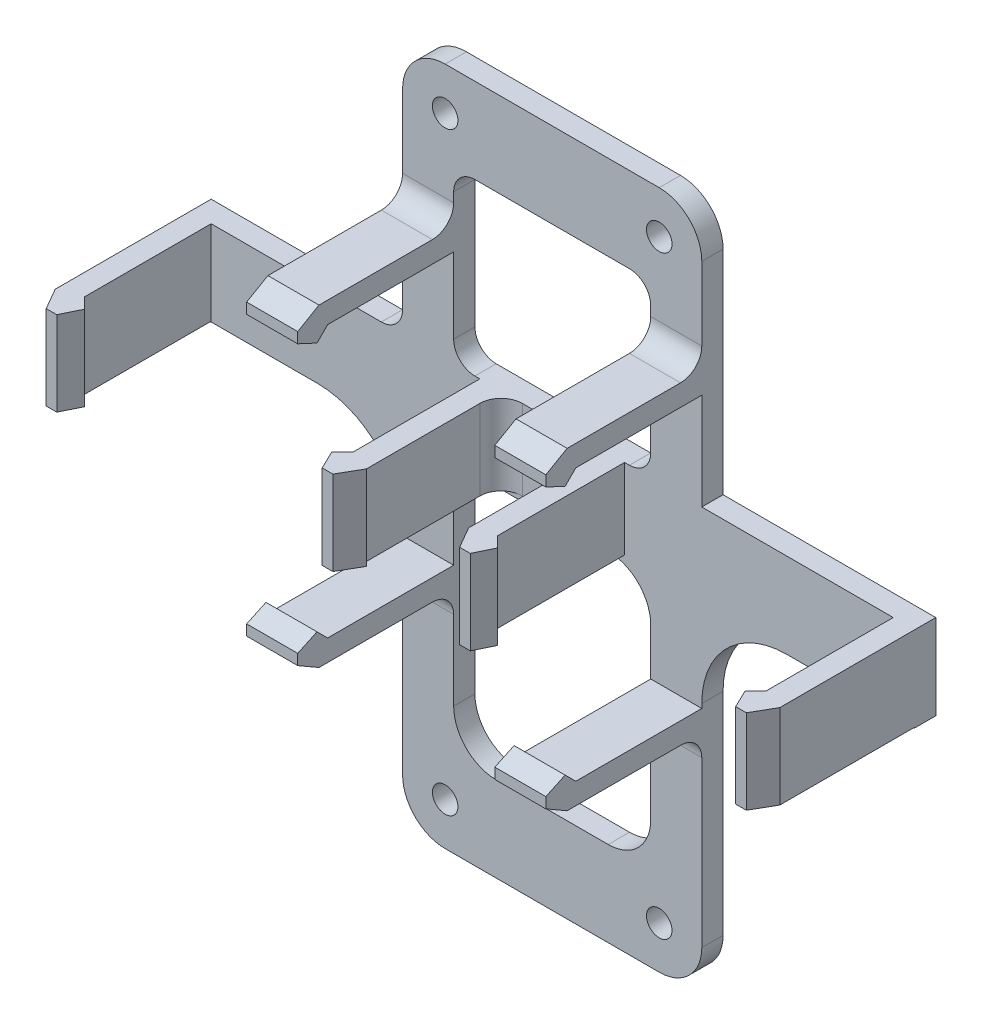
SolidWorks part; units mm, degrees
ref_plane "Front Plane" through (0, 0, 0) normal (0, 0, 1) x (1, 0, 0)
ref_plane "Top Plane" through (0, 0, 0) normal (0, 1, 0) x (1, 0, 0)
ref_plane "Right Plane" through (0, 0, 0) normal (1, 0, 0) x (0, 0, -1)
sketch "Sketch1" plane through (0, 0, 0) normal (0, 0, 1) x (1, 0, 0)
  line L0 (109.4486, 101.4064) -> (109.4486, 0) construction
  line L1 (160.3502, 101.4064) -> (58.547, 101.4064) construction
  line L2 (0, 0) -> (218.8972, 0) construction
  line L3 (87.122, 101.4064) -> (99.822, 101.4064)
  line L4 (58.547, 101.4064) -> (83.947, 101.4064) construction
  line L5 (94.742, 88.7064) -> (94.742, 63.3064)
  line L6 (94.742, 63.3064) -> (124.1552, 63.3064)
  line L7 (87.122, 101.4064) -> (87.122, 63.3064)
  line L8 (87.122, 63.3064) -> (55.372, 63.3064)
  line L9 (87.122, 37.9064) -> (87.122, 6.35)
  line L10 (93.472, 0) -> (109.4486, 0)
  line L11 (55.372, 63.3064) -> (55.372, 50.6064)
  line L12 (55.372, 50.6064) -> (74.422, 50.6064)
  line L13 (83.947, 101.4064) -> (83.947, 0) construction
  line L14 (58.547, 101.4064) -> (160.3502, 101.4064) construction
  line L15 (58.547, 101.4064) -> (58.547, 0) construction
  line L16 (163.5252, 50.6064) -> (144.4752, 50.6064)
  line L17 (163.5252, 63.3064) -> (163.5252, 50.6064)
  line L18 (131.7752, 37.9064) -> (131.7752, 6.35)
  line L19 (131.7752, 63.3064) -> (163.5252, 63.3064)
  line L20 (131.7752, 101.4064) -> (131.7752, 63.3064)
  line L21 (124.1552, 88.7064) -> (124.1552, 63.3064)
  line L22 (131.7752, 101.4064) -> (119.0752, 101.4064)
  line L23 (109.4486, 0) -> (125.4252, 0)
  line L24 (101.092, 50.6064) -> (117.8052, 50.6064)
  line L25 (94.742, 44.2564) -> (94.742, 19.05)
  line L26 (101.092, 12.7) -> (117.8052, 12.7)
  line L27 (124.1552, 44.2564) -> (124.1552, 19.05)
  line L28 (94.742, 50.6064) -> (124.1552, 12.7) construction
  line L29 (94.742, 12.7) -> (124.1552, 50.6064) construction
  line L30 (87.122, 6.35) -> (131.7752, 6.35) construction
  line L32 (99.822, 101.4064) -> (119.0752, 101.4064)
  line L34 (94.742, 88.7064) -> (124.1552, 88.7064)
  circle A0 centre (93.472, 95.0564) radius 1.905
  circle A1 centre (125.4252, 95.0564) radius 1.905
  circle A2 centre (93.472, 6.35) radius 1.905
  circle A3 centre (125.4252, 6.35) radius 1.905
  arc A4 (144.4752, 50.6064) -> (131.7752, 37.9064) centre (144.4752, 37.9064) ccw
  arc A5 (74.422, 50.6064) -> (87.122, 37.9064) centre (74.422, 37.9064) cw
  arc A6 (131.7752, 6.35) -> (125.4252, 0) centre (125.4252, 6.35) cw
  arc A7 (87.122, 6.35) -> (93.472, 0) centre (93.472, 6.35) ccw
  arc A8 (94.742, 19.05) -> (101.092, 12.7) centre (101.092, 19.05) ccw
  arc A9 (117.8052, 12.7) -> (124.1552, 19.05) centre (117.8052, 19.05) ccw
  arc A10 (117.8052, 50.6064) -> (124.1552, 44.2564) centre (117.8052, 44.2564) cw
  arc A11 (101.092, 50.6064) -> (94.742, 44.2564) centre (101.092, 44.2564) ccw
  point P18 (109.4486, 31.6532)
  point P29 (109.4486, 63.3064)
  point P48 (131.7752, 50.6064)
  point P51 (87.122, 50.6064)
  point P54 (131.7752, 0)
  point P57 (87.122, 0)
  point P72 (0, 0)
  point P73 (100.4832, 63.3064)
  dimension "D11" = 6.35
  dimension "D12" = 3.81
  dimension "D13" = 6.35
  dimension "D18" = 12.7
  dimension "D19" = 6.35
  dimension "D1" = 12.7
  dimension "D2" = 12.7
  dimension "D3" = 3.175
  dimension "D4" = 12.7
  dimension "D5" = 38.1
  dimension "D6" = 3.175
  dimension "D7" = 12.7
  dimension "D8" = 7.62
  dimension "D9" = 12.7
  dimension "D10" = 6.35
  dimension "D14" = 6.35
  dimension "D15" = 6.35
  dimension "D16" = 6.35
  dimension "D17" = 6.35
  dimension "D20" = 7.62
extrude "Boss-Extrude1" add sketch "Sketch1" along normal blind 3.175
sketch "Sketch2" plane through (0, 0, 3.175) normal (0, 0, 1) x (1, 0, 0)
  line L0 (58.547, 101.4064) -> (58.547, 0) construction
  line L1 (55.372, 63.3064) -> (58.547, 63.3064)
  line L2 (55.372, 63.3064) -> (55.372, 50.7032)
  line L3 (55.372, 50.7032) -> (58.547, 50.7032)
  line L4 (58.547, 63.3064) -> (58.547, 50.7032)
  line L5 (98.647, 72.765) -> (98.647, 52.765) construction
  line L6 (98.647, 72.765) -> (98.647, 52.765) construction
  line L7 (124.1552, 63.3064) -> (94.742, 63.3064) construction
  line L8 (101.822, 63.3064) -> (98.647, 63.3064)
  line L9 (101.822, 63.3064) -> (101.822, 51.34)
  line L10 (101.822, 51.34) -> (98.647, 51.34)
  line L11 (98.647, 63.3064) -> (98.647, 51.34)
  line L12 (98.647, 52.765) -> (98.647, 49.915) construction
  line L13 (87.122, 37.9064) -> (87.122, 6.35) construction
  line L14 (87.122, 37.265) -> (94.742, 37.265)
  line L15 (87.122, 37.265) -> (87.122, 34.09)
  line L16 (87.122, 34.09) -> (94.742, 34.09)
  line L17 (94.742, 37.265) -> (94.742, 34.09)
  line L18 (94.742, 44.2564) -> (94.742, 19.05) construction
  line L19 (92.2439, 37.265) -> (66.5315, 37.265) construction
  line L20 (92.2439, 37.265) -> (66.5315, 37.265) construction
  line L28 (87.122, 101.4064) -> (87.122, 63.3064) construction
  line L29 (87.122, 80.94) -> (94.742, 80.94)
  line L30 (87.122, 80.94) -> (87.122, 77.765)
  line L31 (87.122, 77.765) -> (94.742, 77.765)
  line L32 (94.742, 80.94) -> (94.742, 77.765)
  line L33 (62.547, 77.765) -> (94.647, 77.765) construction
extrude "Boss-Extrude2" add sketch "Sketch2" along normal up to surface (20.1 mm away)
sketch "Sketch3" plane through (0, 63.3064, 0) normal (0, 1, 0) x (1, 0, 0)
  line L0 (58.547, -22.1034) -> (60.1345, -23.6909)
  line L1 (58.547, -23.275) -> (58.547, -3.175) construction
  line L2 (60.1345, -23.6909) -> (58.7926, -26.45)
  line L3 (58.7926, -26.45) -> (57.2051, -26.45)
  line L4 (57.2051, -26.45) -> (55.372, -23.275)
  line L5 (58.547, -23.275) -> (55.372, -23.275) construction
  line L6 (58.547, -22.1034) -> (58.547, -23.275)
  line L7 (58.547, -23.275) -> (55.372, -23.275)
  line L8 (58.547, -23.275) -> (98.647, -23.275) construction
  line L9 (78.597, -23.275) -> (78.597, -3.175) construction
  line L10 (87.122, -3.175) -> (58.547, -3.175) construction
  line L11 (98.647, -22.1034) -> (97.0595, -23.6909)
  line L12 (98.647, -22.1034) -> (98.647, -23.275)
  line L13 (98.647, -23.275) -> (101.822, -23.275)
  line L14 (99.9889, -26.45) -> (101.822, -23.275)
  line L15 (98.4014, -26.45) -> (99.9889, -26.45)
  line L16 (97.0595, -23.6909) -> (98.4014, -26.45)
  arc A0 (60.547, -19.275) -> (62.547, -21.275) centre (60.547, -21.275) ccw construction
  arc A1 (60.547, -19.275) -> (62.547, -21.275) centre (60.547, -21.275) ccw construction
  dimension "D1" = 3.175
  dimension "D2" = 1.5875
  dimension "D3" = 60
  dimension "D4" = 45
  dimension "D5" = 1.5875
extrude "Boss-Extrude3" add sketch "Sketch3" against normal up to surface (12.6032 mm away) up to face at (56.9595, 50.7032, 13.225)
sketch "Sketch4" plane through (87.122, 0, 0) normal (-1, 0, 0) x (0, 0, 1)
  line L6 (23.275, 80.94) -> (23.275, 77.765)
  line L7 (23.275, 77.765) -> (21.9821, 77.765)
  line L8 (23.275, 77.765) -> (3.175, 77.765) construction
  line L9 (21.9821, 77.765) -> (23.5696, 76.1775)
  line L10 (23.5696, 76.1775) -> (26.45, 77.5194)
  line L11 (26.45, 77.5194) -> (26.45, 79.1069)
  line L12 (26.45, 79.1069) -> (23.275, 80.94)
  line L13 (23.275, 77.765) -> (23.275, 37.265) construction
  line L14 (23.275, 57.515) -> (0, 57.515) construction
  line L15 (0, 0) -> (0, 101.4064) construction
  line L16 (26.45, 35.9231) -> (23.275, 34.09)
  line L17 (26.45, 37.5106) -> (26.45, 35.9231)
  line L18 (23.5696, 38.8525) -> (26.45, 37.5106)
  line L19 (21.9821, 37.265) -> (23.5696, 38.8525)
  line L20 (23.275, 37.265) -> (21.9821, 37.265)
  line L21 (23.275, 34.09) -> (23.275, 37.265)
  arc A0 (23.275, 76.265) -> (22.775, 76.765) centre (22.775, 76.265) ccw construction
  dimension "D1" = 45
  dimension "D2" = 60
  dimension "D3" = 3.175
  dimension "D4" = 1.5875
  dimension "D5" = 1.5875
extrude "Boss-Extrude4" add sketch "Sketch4" against normal up to surface (7.62 mm away) up to face at (94.742, 77.6794, 7.4063)
ref_plane "Plane1" through (109.4486, 0, 0) normal (-1, 0, 0) x (0, 0, 1)
fillet "Fillet1" radius 6.35 2 edges at (87.122, 101.4064, 1.5875) (131.7752, 101.4064, 1.5875)
mirror "Mirror3" about plane through (109.4486, 0, 0) normal (-1, 0, 0) of "Boss-Extrude2", "Boss-Extrude3", "Boss-Extrude4"
fillet "Fillet2" radius 3.175 11 edges at (90.932, 34.09, 3.175) (101.822, 57.3232, 3.175) (90.932, 80.94, 3.175) (87.122, 63.3064, 1.5875) (94.742, 63.3064, 1.5875) (94.742, 88.7064, 1.5875) (124.1552, 63.3064, 1.5875) (124.1552, 88.7064, 1.5875) (127.9652, 34.09, 3.175) (127.9652, 80.94, 3.175) (117.0752, 57.3232, 3.175)
